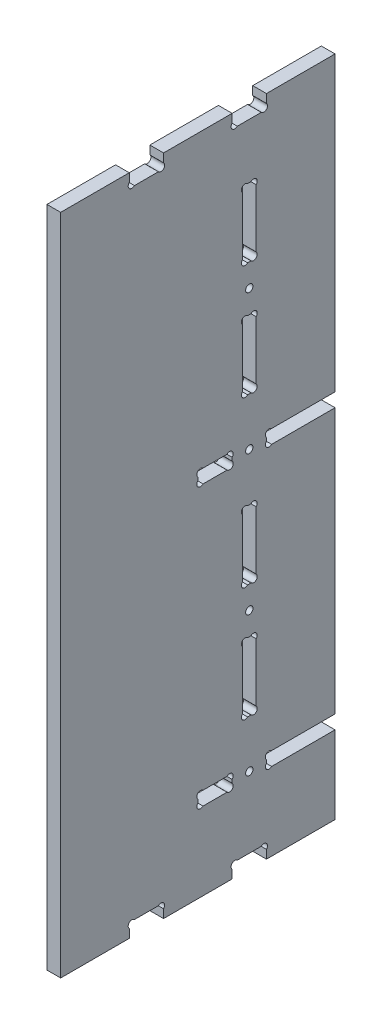
SolidWorks part; units mm, degrees
ref_plane "Plan de face" through (0, 0, 0) normal (0, 0, 1) x (1, 0, 0)
ref_plane "Plan de dessus" through (0, 0, 0) normal (0, 1, 0) x (1, 0, 0)
ref_plane "Plan de droite" through (0, 0, 0) normal (1, 0, 0) x (0, 0, -1)
sketch "Esquisse1" plane through (0, 0, 0) normal (1, 0, 0) x (0, 0, -1)
  line L0 (-10, 0) -> (130, 0) construction
  line L1 (0, -10) -> (0, 300) construction
  line L2 (120, -10) -> (120, 300) construction
  line L3 (130, 290) -> (-10, 290) construction
  line L4 (-20, 34) -> (140, 34) construction
  line L5 (-20, 40) -> (140, 40) construction
  line L6 (140, 156) -> (-20, 156) construction
  line L7 (-20, 162) -> (140, 162) construction
  line L8 (-10, 284) -> (130, 284) construction
  line L9 (130, 6) -> (-10, 6) construction
  line L10 (-20, 256) -> (140, 256) construction
  line L11 (60, 320.0265) -> (60, -23.3948) construction
  line L12 (-59.0456, 145) -> (186.4267, 145) construction
  line L13 (30, -9.1701) -> (30, 14.8573) construction
  line L14 (45, 11.6889) -> (45, -9.1701) construction
  line L15 (37.5, 2.4409) -> (37.5, -4.0751) construction
  line L16 (30, 6) -> (42.8913, -6.8913) construction
  line L17 (32.2627, 6) -> (42.7373, 6)
  line L18 (45, 3.7373) -> (45, 0)
  line L19 (30, 3.7373) -> (30, 0)
  line L20 (75, 3.7373) -> (75, 0)
  line L21 (87.7373, 6) -> (77.2627, 6)
  line L22 (90, 3.7373) -> (90, 0)
  line L23 (0, 0) -> (30, 0)
  line L24 (45, 0) -> (75, 0)
  line L25 (90, 0) -> (120, 0)
  line L26 (90, 290) -> (120, 290)
  line L27 (90, 286.2627) -> (90, 290)
  line L28 (87.7373, 284) -> (77.2627, 284)
  line L29 (75, 286.2627) -> (75, 290)
  line L30 (45, 290) -> (75, 290)
  line L31 (45, 286.2627) -> (45, 290)
  line L32 (32.2627, 284) -> (42.7373, 284)
  line L33 (30, 286.2627) -> (30, 290)
  line L34 (0, 290) -> (30, 290)
  line L35 (0, 290) -> (0, 0)
  line L36 (120, 0) -> (120, 34)
  line L37 (-20, 134) -> (140, 134) construction
  line L38 (90, 310.1112) -> (90, -15.2075) construction
  line L39 (70.8381, 37) -> (93.292, 37) construction
  line L40 (79.681, 98) -> (95, 98) construction
  line L41 (90, 34) -> (99.2543, 43.2543) construction
  line L42 (90, 37.7373) -> (90, 36.2627)
  line L43 (92.2627, 40) -> (120, 40)
  line L44 (92.2627, 34) -> (120, 34)
  line L45 (120, 40) -> (120, 156)
  line L46 (92.2627, 162) -> (120, 162)
  line L47 (92.2627, 156) -> (120, 156)
  line L48 (90, 158.2627) -> (90, 159.7373)
  line L49 (120, 162) -> (120, 290)
  line L50 (82.5, -10) -> (82.5, 300) construction
  line L51 (75, 43.6727) -> (75, 30.1815) construction
  line L52 (67.5, 38.4171) -> (67.5, 35.1314) construction
  line L53 (75, 37.7373) -> (75, 36.2627)
  line L54 (60, 37.7373) -> (60, 36.2627)
  line L55 (62.2627, 40) -> (72.7373, 40)
  line L56 (72.7373, 34) -> (62.2627, 34)
  line L57 (60, 158.2627) -> (60, 159.7373)
  line L58 (72.7373, 162) -> (62.2627, 162)
  line L59 (62.2627, 156) -> (72.7373, 156)
  line L60 (75, 158.2627) -> (75, 159.7373)
  line L61 (79.5, 164.7795) -> (79.5, 25.9693) construction
  line L62 (85.5, 164.7795) -> (85.5, 25.9693) construction
  line L63 (97.4677, 88) -> (51.1707, 88) construction
  line L64 (97.4677, 58) -> (51.1707, 58) construction
  line L65 (79.5, 88) -> (87.7395, 79.7605) construction
  line L66 (77.6869, 73) -> (86.5883, 73) construction
  line L67 (83.2373, 138) -> (81.7627, 138)
  line L68 (83.2373, 58) -> (81.7627, 58)
  line L69 (85.5, 60.2627) -> (85.5, 85.7373)
  line L70 (83.2373, 88) -> (81.7627, 88)
  line L71 (79.5, 60.2627) -> (79.5, 85.7373)
  line L72 (85.5, 135.7373) -> (85.5, 110.2627)
  line L73 (79.5, 135.7373) -> (79.5, 110.2627)
  line L74 (83.2373, 108) -> (81.7627, 108)
  line L75 (66.7218, 159) -> (108.1831, 159) construction
  line L76 (85.5, 257.7373) -> (85.5, 232.2627)
  line L77 (79.5, 257.7373) -> (79.5, 232.2627)
  line L78 (83.2373, 260) -> (81.7627, 260)
  line L79 (83.2373, 230) -> (81.7627, 230)
  line L80 (83.2373, 210) -> (81.7627, 210)
  line L81 (85.5, 182.2627) -> (85.5, 207.7373)
  line L82 (79.5, 182.2627) -> (79.5, 207.7373)
  line L83 (83.2373, 180) -> (81.7627, 180)
  arc A0 (32.2627, 6) -> (30, 3.7373) centre (31.1314, 4.8686) ccw
  arc A1 (42.7373, 6) -> (45, 3.7373) centre (43.8686, 4.8686) cw
  arc A2 (77.2627, 6) -> (75, 3.7373) centre (76.1314, 4.8686) ccw
  arc A3 (87.7373, 6) -> (90, 3.7373) centre (88.8686, 4.8686) cw
  arc A4 (87.7373, 284) -> (90, 286.2627) centre (88.8686, 285.1314) ccw
  arc A5 (77.2627, 284) -> (75, 286.2627) centre (76.1314, 285.1314) cw
  arc A6 (42.7373, 284) -> (45, 286.2627) centre (43.8686, 285.1314) ccw
  arc A7 (32.2627, 284) -> (30, 286.2627) centre (31.1314, 285.1314) cw
  arc A8 (90, 36.2627) -> (92.2627, 34) centre (91.1314, 35.1314) ccw
  arc A9 (90, 37.7373) -> (92.2627, 40) centre (91.1314, 38.8686) cw
  arc A10 (90, 158.2627) -> (92.2627, 156) centre (91.1314, 157.1314) ccw
  arc A11 (90, 159.7373) -> (92.2627, 162) centre (91.1314, 160.8686) cw
  circle A12 centre (82.5, 37) radius 1.6
  circle A13 centre (82.5, 159) radius 1.6
  arc A14 (75, 36.2627) -> (72.7373, 34) centre (73.8686, 35.1314) cw
  arc A15 (75, 37.7373) -> (72.7373, 40) centre (73.8686, 38.8686) ccw
  arc A16 (60, 36.2627) -> (62.2627, 34) centre (61.1314, 35.1314) ccw
  arc A17 (60, 37.7373) -> (62.2627, 40) centre (61.1314, 38.8686) cw
  arc A18 (60, 158.2627) -> (62.2627, 156) centre (61.1314, 157.1314) ccw
  arc A19 (60, 159.7373) -> (62.2627, 162) centre (61.1314, 160.8686) cw
  arc A20 (75, 158.2627) -> (72.7373, 156) centre (73.8686, 157.1314) cw
  arc A21 (75, 159.7373) -> (72.7373, 162) centre (73.8686, 160.8686) ccw
  arc A22 (81.7627, 88) -> (79.5, 85.7373) centre (80.6314, 86.8686) ccw
  arc A23 (83.2373, 88) -> (85.5, 85.7373) centre (84.3686, 86.8686) cw
  arc A24 (81.7627, 58) -> (79.5, 60.2627) centre (80.6314, 59.1314) cw
  arc A25 (83.2373, 58) -> (85.5, 60.2627) centre (84.3686, 59.1314) ccw
  arc A26 (81.7627, 138) -> (79.5, 135.7373) centre (80.6314, 136.8686) ccw
  arc A27 (83.2373, 138) -> (85.5, 135.7373) centre (84.3686, 136.8686) cw
  arc A28 (81.7627, 108) -> (79.5, 110.2627) centre (80.6314, 109.1314) cw
  arc A29 (83.2373, 108) -> (85.5, 110.2627) centre (84.3686, 109.1314) ccw
  circle A30 centre (82.5, 98) radius 1.6
  arc A31 (83.2373, 230) -> (85.5, 232.2627) centre (84.3686, 231.1314) ccw
  arc A32 (81.7627, 260) -> (79.5, 257.7373) centre (80.6314, 258.8686) ccw
  arc A33 (83.2373, 260) -> (85.5, 257.7373) centre (84.3686, 258.8686) cw
  arc A34 (81.7627, 230) -> (79.5, 232.2627) centre (80.6314, 231.1314) cw
  circle A35 centre (82.5, 220) radius 1.6
  arc A36 (81.7627, 210) -> (79.5, 207.7373) centre (80.6314, 208.8686) ccw
  arc A37 (83.2373, 210) -> (85.5, 207.7373) centre (84.3686, 208.8686) cw
  arc A38 (81.7627, 180) -> (79.5, 182.2627) centre (80.6314, 181.1314) cw
  arc A39 (83.2373, 180) -> (85.5, 182.2627) centre (84.3686, 181.1314) ccw
  dimension "D4" = 34
  dimension "D12" = 3
  dimension "D7" = 7.5
  dimension "D17" = 15
  dimension "D1" = 15
  dimension "D2" = 7.5
  dimension "D3" = 45
  dimension "D5" = 34
  dimension "D6" = 100
  dimension "D8" = 7.5
  dimension "D9" = 6
  dimension "D10" = 3
  dimension "D11" = 45
  dimension "D13" = 6
  dimension "D14" = 10
  dimension "D15" = 30
  dimension "D16" = 45
extrude "Extrusion1" add sketch "Esquisse1" along normal blind 6
